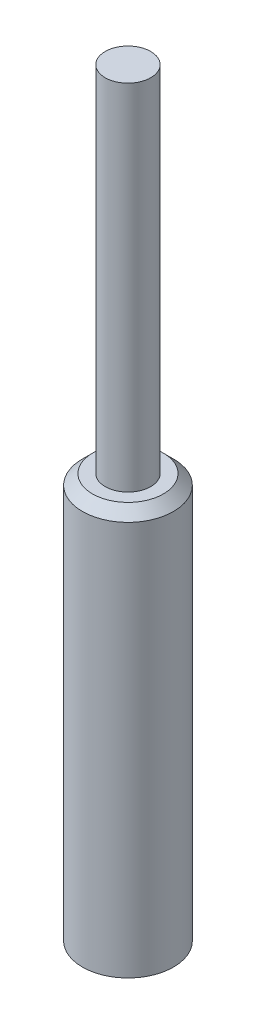
SolidWorks part; units mm, degrees
material "Простая углеродистая сталь"
ref_plane "Front Plane" through (0, 0, 0) normal (0, 0, 1) x (1, 0, 0)
ref_plane "Top Plane" through (0, 0, 0) normal (0, 1, 0) x (1, 0, 0)
ref_plane "Right Plane" through (0, 0, 0) normal (1, 0, 0) x (0, 0, -1)
sketch "Эскиз1" plane through (0, 0, 0) normal (0, 0, 1) x (1, 0, 0)
  line L0 (0, 0) -> (0, -6.2208) construction
  line L1 (0, 0) -> (-0.9, 0)
  line L2 (-0.9, 0) -> (-0.9, 8)
  line L3 (-0.9, 8) -> (-0.45, 8)
  line L4 (-0.45, 8) -> (-0.45, 15)
  line L5 (-0.45, 15) -> (0, 15)
  line L6 (0, 15) -> (0, 0)
  dimension "D1" = 7
  dimension "D2" = 0.9
  dimension "D3" = 1.8
  dimension "D4" = 8
revolve "Повернуть1" add sketch "Эскиз1" angle 360 about L0
chamfer "Фаска1" distance 0.2 angle 45 1 edges at (0, 8, 0.9)
